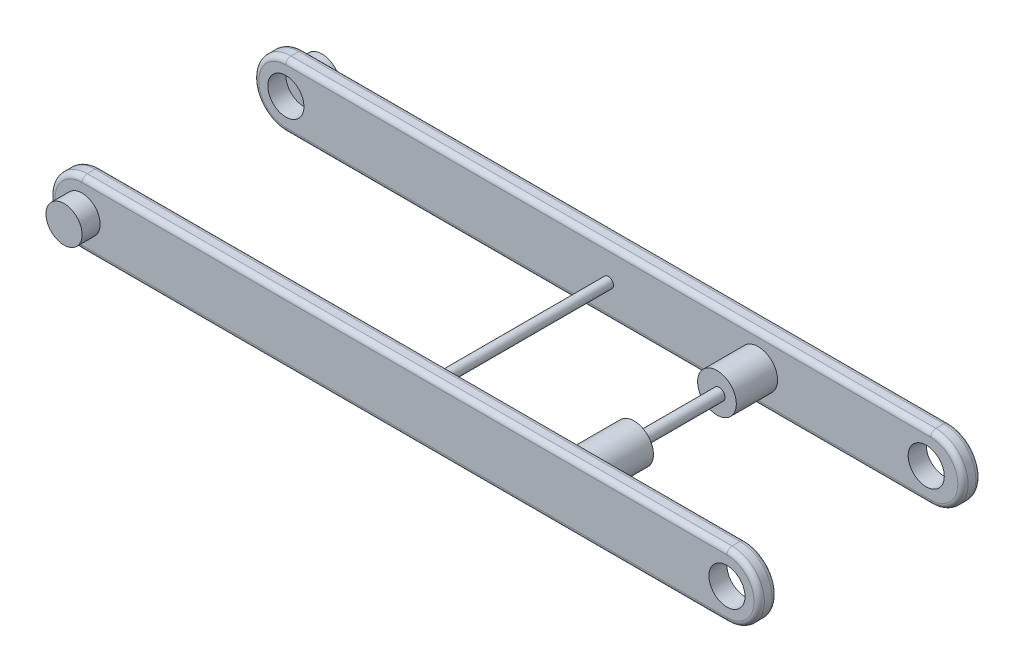
SolidWorks part; units mm, degrees
ref_plane "Front Plane" through (0, 0, 0) normal (0, 0, 1) x (1, 0, 0)
ref_plane "Top Plane" through (0, 0, 0) normal (0, 1, 0) x (1, 0, 0)
ref_plane "Right Plane" through (0, 0, 0) normal (1, 0, 0) x (0, 0, -1)
sketch "Sketch1" plane through (0, 0, 0) normal (0, 0, 1) x (1, 0, 0)
  line L0 (-125, 0) -> (125, 0) construction
  line L1 (-125, 12.5) -> (125, 12.5)
  line L2 (-125, -12.5) -> (125, -12.5)
  arc A0 (-125, 12.5) -> (-125, -12.5) centre (-125, 0) ccw
  arc A1 (125, -12.5) -> (125, 12.5) centre (125, 0) ccw
  point P2 (0, 0)
  dimension "D1" = 250
  dimension "D2" = 25
extrude "Boss-Extrude1" add sketch "Sketch1" along normal blind 7
sketch "Sketch2" plane through (0, 0, 7) normal (0, 0, 1) x (1, 0, 0)
  circle A0 centre (-125, 0) radius 7
  dimension "D1" = 14
extrude "Cut-Extrude1" cut sketch "Sketch2" against normal blind 7 contours A0
sketch "Sketch3" plane through (0, 0, 7) normal (0, 0, 1) x (1, 0, 0)
  circle A0 centre (123.251, 0) radius 7
  dimension "D1" = 14
extrude "Cut-Extrude2" cut sketch "Sketch3" against normal blind 7
ref_plane "Plane1" through (0, 0, 79) normal (0, 0, 1) x (1, 0, 0)
sketch "Sketch4" plane through (0, 0, 79) normal (0, 0, 1) x (1, 0, 0)
  line L0 (125, 0) -> (-125, 0) construction
  line L1 (125, -12.5) -> (-125, -12.5)
  line L2 (125, 12.5) -> (-125, 12.5)
  arc A0 (125, -12.5) -> (125, 12.5) centre (125, 0) ccw
  arc A1 (-125, 12.5) -> (-125, -12.5) centre (-125, 0) ccw
  point P2 (0, 0)
  dimension "D1" = 250
  dimension "D2" = 250
  dimension "D3" = 25
extrude "Boss-Extrude2" add sketch "Sketch4" along normal blind 7 separate body
sketch "Sketch5" plane through (0, 0, 86) normal (0, 0, 1) x (1, 0, 0)
  circle A0 centre (125, 0) radius 7
  circle A1 centre (-125, 0) radius 7
  dimension "D1" = 14
  dimension "D2" = 14
extrude "Cut-Extrude3" cut sketch "Sketch5" against normal blind 7
sketch "Sketch6" plane through (0, 0, 86) normal (0, 0, 1) x (1, 0, 0)
  circle A0 centre (-125, 0) radius 7
extrude "Boss-Extrude3" add sketch "Sketch6" along normal blind 7 separate body
sketch "Sketch8" plane through (0, 0, 0) normal (0, 0, -1) x (-1, 0, 0)
  circle A0 centre (125, 0) radius 7.2121
extrude "Boss-Extrude4" add sketch "Sketch8" along normal blind 7
fillet "Fillet1" radius 2 8 edges at (-137.5, 0, 86) (0, 12.5, 86) (137.5, 0, 86) (137.5, 0, 79) (0, -12.5, 79) (-137.5, 0, 79) (0, -12.5, 86) (0, 12.5, 79)
fillet "Fillet2" radius 2 8 edges at (137.5, 0, 7) (0, -12.5, 7) (-137.5, 0, 7) (137.5, 0, 0) (0, -12.5, 0) (-137.5, 0, 0) (0, 12.5, 7) (0, 12.5, 0)
sketch "Sketch9" plane through (0, 0, 0) normal (0, 0, -1) x (-1, 0, 0)
  line L0 (125, 0) -> (0, 0) construction
  circle A0 centre (0, 0) radius 2
  dimension "D1" = 4
extrude "Boss-Extrude5" add sketch "Sketch9" against normal blind 82
sketch "Sketch10" plane through (0, 0, 0) normal (0, 0, -1) x (-1, 0, 0)
  line L0 (0, 0) -> (-118, 0) construction
  circle A0 centre (-125, 0) radius 7 construction
  circle A1 centre (-59, 0) radius 2.25
  dimension "D1" = 4.5
extrude "Boss-Extrude6" add sketch "Sketch10" against normal blind 82
sketch "Sketch11" plane through (0, 0, 0) normal (0, 0, -1) x (-1, 0, 0)
  line L0 (0, 0) -> (-116.251, 0) construction
  circle A0 centre (-123.251, 0) radius 7 construction
  circle A1 centre (-58.1255, 0) radius 7.5
  point P5 (-58.1255, 0)
  dimension "D1" = 15
extrude "Boss-Extrude7" add sketch "Sketch11" against normal blind 23
sketch "Sketch12" plane through (0, 0, 79) normal (0, 0, -1) x (-1, 0, 0)
  line L0 (0, 0) -> (-118, 0) construction
  circle A0 centre (-125, 0) radius 7 construction
  circle A1 centre (-59, 0) radius 7.5
  point P6 (-59, 0)
  dimension "D1" = 15
extrude "Boss-Extrude8" add sketch "Sketch12" along normal blind 23
